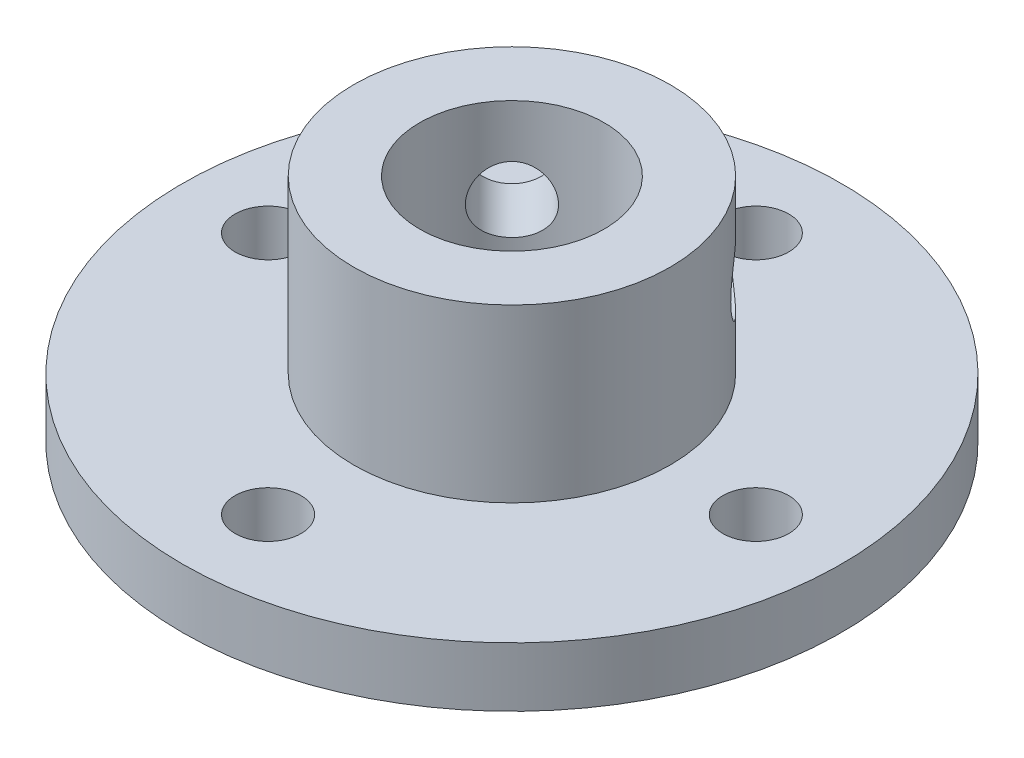
SolidWorks part; units mm, degrees
ref_plane "Front Plane" through (0, 0, 0) normal (0, 0, 1) x (1, 0, 0)
ref_plane "Top Plane" through (0, 0, 0) normal (0, 1, 0) x (1, 0, 0)
ref_plane "Right Plane" through (0, 0, 0) normal (1, 0, 0) x (0, 0, -1)
ref_plane "Plane1" through (0, 0, 0) normal (-0.7071, 0, 0.7071) x (0.7071, 0, 0.7071)
sketch "Sketch1" plane through (0, 0, 0) normal (0, 1, 0) x (1, 0, 0)
  circle A0 centre (0, 0) radius 25
  dimension "D1" = 50
extrude "Boss-Extrude1" add sketch "Sketch1" along normal blind 4.5
sketch "Sketch2" plane through (0, 4.5, 0) normal (0, 1, 0) x (1, 0, 0)
  circle A0 centre (0, 0) radius 12
  dimension "D1" = 24
extrude "Boss-Extrude2" add sketch "Sketch2" along normal blind 13
sketch "Sketch3" plane through (0, 17.5, 0) normal (0, 1, 0) x (1, 0, 0)
  circle A0 centre (0, 0) radius 7
  dimension "D1" = 14
extrude "Cut-Extrude1" cut sketch "Sketch3" against normal up to surface (17.5 mm away) up to face at (0, 0, 25)
sketch "Sketch4" plane through (0, 4.5, 0) normal (0, 1, 0) x (1, 0, 0)
  circle A0 centre (0, 0) radius 18.5 construction
  circle A1 centre (-18.5, 0) radius 2.5
  circle A2 centre (0, 18.5) radius 2.5
  circle A3 centre (18.5, 0) radius 2.5
  circle A4 centre (0, -18.5) radius 2.5
  dimension "D1" = 37
  dimension "D2" = 5
extrude "Cut-Extrude2" cut sketch "Sketch4" against normal up to surface (4.5 mm away) up to face at (0, 0, 7)
sketch "Sketch5" plane through (0, 0, 0) normal (-0.7071, 0, 0.7071) x (0.7071, 0, 0.7071)
  line L0 (0, 17.5) -> (0, 4.5) construction
  line L1 (12, 17.5) -> (-12, 17.5) construction
  line L2 (25, 4.5) -> (-25, 4.5) construction
  circle A0 centre (0, 11) radius 2.5
  dimension "D1" = 5
extrude "Cut-Extrude3" cut sketch "Sketch5" against normal blind 25
pattern_circular "CirPattern1" count 2 every 90 about axis through (0, 17.5, 0) along (0, 1, 0) of "Cut-Extrude3"
